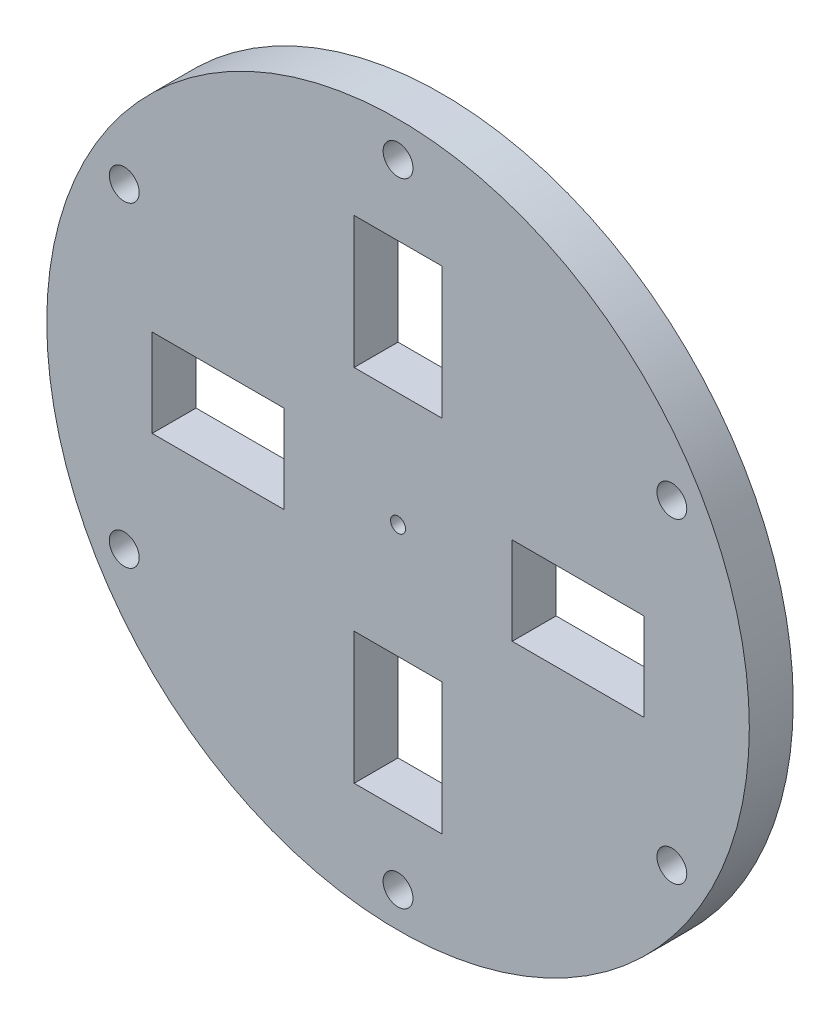
SolidWorks part; units mm, degrees
ref_plane "Front Plane" through (0, 0, 0) normal (0, 0, 1) x (1, 0, 0)
ref_plane "Top Plane" through (0, 0, 0) normal (0, 1, 0) x (1, 0, 0)
ref_plane "Right Plane" through (0, 0, 0) normal (1, 0, 0) x (0, 0, -1)
sketch "Sketch1" plane through (0, 0, 0) normal (0, 0, 1) x (1, 0, 0)
  circle A0 centre (0, 0) radius 40
  circle A1 centre (0, 0) radius 0.75
  dimension "D1" = 80
  dimension "D2" = 1.5
extrude "Boss-Extrude1" add sketch "Sketch1" along normal blind 5
sketch "Sketch4" plane through (0, 0, 5) normal (0, 0, 1) x (1, 0, 0)
  line L0 (0, 1040) -> (0, 28) construction
  line L1 (0, 0) -> (40, 0) construction
  line L2 (-5, 28) -> (-5, 13)
  line L3 (-5, 28) -> (5, 28)
  line L4 (13, 5) -> (13, -5)
  line L5 (-5, 13) -> (5, 13)
  line L6 (5, 28) -> (5, 13)
  line L7 (0, 13) -> (0, -40) construction
  line L8 (28, 5) -> (13, 5)
  line L9 (28, -5) -> (13, -5)
  line L10 (28, 5) -> (28, -5)
  line L11 (5, -13) -> (-5, -13)
  line L12 (5, -28) -> (5, -13)
  line L13 (-5, -28) -> (-5, -13)
  line L14 (5, -28) -> (-5, -28)
  line L15 (-13, -5) -> (-13, 5)
  line L16 (-28, -5) -> (-13, -5)
  line L17 (-28, 5) -> (-13, 5)
  line L18 (-28, -5) -> (-28, 5)
  point P12 (0, 0)
  dimension "D1" = 15
  dimension "D2" = 10
  dimension "D3" = 4
  dimension "D4" = 13
extrude "Cut-Extrude3" cut sketch "Sketch4" against normal through all
sketch "Sketch5" plane through (0, 0, 5) normal (0, 0, 1) x (1, 0, 0)
  line L0 (0, 0) -> (0, 40) construction
  circle A2 centre (0, 0) radius 40 construction
  circle A3 centre (0, 36) radius 1.7
  circle A4 centre (31.1769, 18) radius 1.7
  circle A5 centre (31.1769, -18) radius 1.7
  circle A6 centre (0, -36) radius 1.7
  circle A7 centre (-31.1769, -18) radius 1.7
  circle A8 centre (-31.1769, 18) radius 1.7
  dimension "D1" = 3.4
  dimension "D2" = 4
  dimension "D3" = 6
extrude "Cut-Extrude4" cut sketch "Sketch5" against normal through all
sketch "Sketch6" plane through (0, 0, 5) normal (0, 0, 1) x (1, 0, 0)
  circle A0 centre (0, 0) radius 0.85
  circle A1 centre (0, 0) radius 0.75 construction
  dimension "D1" = 0.1
extrude "Cut-Extrude5" cut sketch "Sketch6" against normal through all
